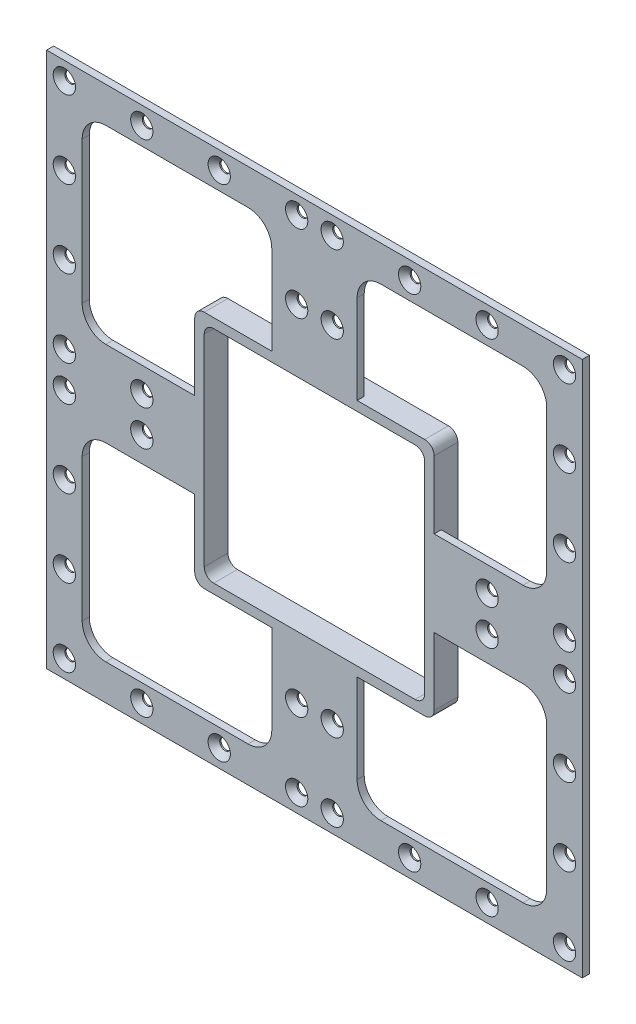
SolidWorks part; units mm, degrees
material "6061-T6 (SS)"
ref_plane "Alzado" through (0, 0, 0) normal (0, 0, 1) x (1, 0, 0)
ref_plane "Planta" through (0, 0, 0) normal (0, 1, 0) x (1, 0, 0)
ref_plane "Vista lateral" through (0, 0, 0) normal (1, 0, 0) x (0, 0, -1)
sketch "Sketch1" plane through (0, 0, 0) normal (0, 0, 1) x (1, 0, 0)
  line L1 (-113, 113) -> (113, 113)
  line L2 (-113, 113) -> (-113, -113)
  line L3 (-113, -113) -> (113, -113)
  line L4 (113, 113) -> (113, -113)
  line L5 (-113, 113) -> (113, -113) construction
  line L6 (-113, -113) -> (113, 113) construction
  point P0 (0, 0)
  dimension "D1" = 226
  dimension "D2" = 226
extrude "Boss-Extrude1" add sketch "Sketch1" along normal blind 3
sketch "Sketch2" plane through (0, 0, 0) normal (0, 0, 1) x (1, 0, 0)
  line L0 (-113, 113) -> (-113, -113) construction
  line L1 (-98, 98) -> (-18, 98)
  line L2 (-98, 98) -> (-98, 18)
  line L3 (-98, 18) -> (-18, 18)
  line L4 (-18, 98) -> (-18, 18)
  line L5 (-98, 98) -> (-18, 18) construction
  line L6 (-98, 18) -> (-18, 98) construction
  line L7 (113, 113) -> (-113, 113) construction
  point P0 (-58, 58)
  point P9 (-58, 98)
  dimension "D1" = 80
  dimension "D2" = 80
  dimension "D3" = 15
  dimension "D4" = 15
extrude "Cut-Extrude2" cut sketch "Sketch2" along normal through all
fillet "Fillet1" radius 10 4 edges at (-98, 98, 1.5) (-18, 98, 1.5) (-18, 18, 1.5) (-98, 18, 1.5)
pattern_linear "LPattern2" count 2 spacing 116 along (0, -1, 0) count 2 spacing 116 along (1, 0, 0) of "Fillet1", "Cut-Extrude2"
sketch "Sketch11" plane through (0, 0, 3) normal (0, 0, 1) x (1, 0, 0)
  line L0 (-113, 113) -> (-113, -113) construction
  line L1 (113, 113) -> (-113, 113) construction
  point P0 (-105.5, 105.5)
  dimension "D1" = 7.5
  dimension "D2" = 7.5
hole_wizard "CSK for M4 Flat Head Machine Screw4" positions "Sketch11" profile "Sketch12" countersink size "M4" standard "ANSI Metric" end condition through all
sketch "Sketch12" plane through (-105.5, 105.5, 3) normal (1, 0, 0) x (0, -1, 0)
  line L0 (0, 0) -> (0, 3)
  line L1 (0, 3) -> (2.25, 3)
  line L2 (2.25, 3) -> (2.25, 2.45)
  line L3 (2.25, 2.45) -> (4.7, 0)
  line L5 (4.7, 0) -> (0, 0)
  line L6 (-2.25, 2.45) -> (-4.7, 0) construction
  line L11 (0, -6.35) -> (0, 107.95) construction
  dimension "Thru Hole Dia." = 4.5
  dimension "Thru Hole Depth" = 3
  dimension "Near C'Sink Dia." = 9.4
  dimension "Near C'Sink Angle" = 90
sketch "Sketch13" plane through (0, 0, 3) normal (0, 0, 1) x (1, 0, 0)
  line L0 (0, 113) -> (0, -113) construction
  line L1 (113, 113) -> (-113, 113) construction
  line L2 (-113, -113) -> (113, -113) construction
  line L3 (-113, 0) -> (113, 0) construction
  line L4 (-113, 113) -> (-113, -113) construction
  line L5 (113, -113) -> (113, 113) construction
pattern_linear "LPattern8" count 4 spacing 32.6667 along (1, 0, 0) count 4 spacing 32.6667 along (0, -1, 0) skipping (1, 1), (1, 2), (2, 1), (2, 2) of "CSK for M4 Flat Head Machine Screw4"
mirror "Mirror1" about plane through (0, 0, 0) normal (1, 0, 0) of "LPattern8", "CSK for M4 Flat Head Machine Screw4" second plane through (0, 0, 0) second plane normal (0, 1, 0)
sketch "Sketch14" plane through (0, 0, 3) normal (0, 0, 1) x (1, 0, 0)
  line L1 (-50.5, 50.5) -> (50.5, 50.5)
  line L2 (-50.5, 50.5) -> (-50.5, -50.5)
  line L3 (-50.5, -50.5) -> (50.5, -50.5)
  line L4 (50.5, 50.5) -> (50.5, -50.5)
  line L5 (-50.5, 50.5) -> (50.5, -50.5) construction
  line L6 (-50.5, -50.5) -> (50.5, 50.5) construction
  point P0 (0, 0)
  dimension "D1" = 101
  dimension "D2" = 101
extrude "Cut-Extrude3" cut sketch "Sketch14" against normal up to next
sketch "Sketch15" plane through (0, 0, 3) normal (0, 0, 1) x (1, 0, 0)
  line L1 (-50.5, 50.5) -> (50.5, 50.5)
  line L2 (-50.5, 50.5) -> (-50.5, -50.5)
  line L3 (-50.5, -50.5) -> (50.5, -50.5)
  line L4 (50.5, 50.5) -> (50.5, -50.5)
  line L5 (-50.5, 50.5) -> (50.5, -50.5) construction
  line L6 (-50.5, -50.5) -> (50.5, 50.5) construction
  line L7 (-46.5, 46.5) -> (46.5, 46.5)
  line L8 (-46.5, 46.5) -> (-46.5, -46.5)
  line L9 (-46.5, -46.5) -> (46.5, -46.5)
  line L10 (46.5, 46.5) -> (46.5, -46.5)
  line L11 (-46.5, 46.5) -> (46.5, -46.5) construction
  line L12 (-46.5, -46.5) -> (46.5, 46.5) construction
  point P0 (0, 0)
  point P6 (0, 0)
  dimension "D1" = 101
  dimension "D2" = 4
extrude "Boss-Extrude2" add sketch "Sketch15" against normal blind 10
fillet "Fillet2" radius 4 8 edges at (-46.5, -46.5, -2) (-50.5, -50.5, -2) (46.5, -46.5, -2) (50.5, -50.5, -2) (46.5, 46.5, -2) (50.5, 50.5, -2) (-46.5, 46.5, -2) (-50.5, 50.5, -2)
